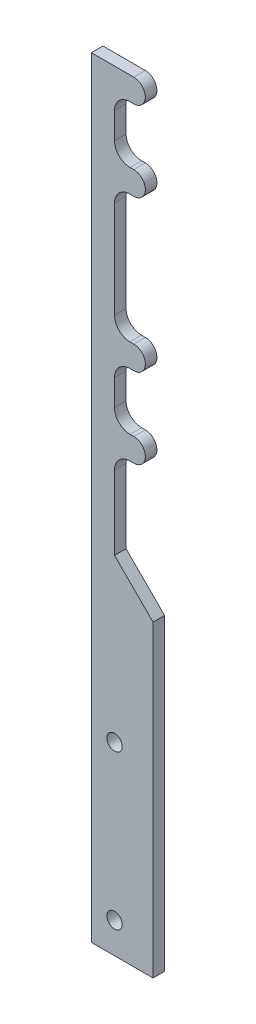
SolidWorks part; units mm, degrees
material "3003 Alloy"
ref_plane "Front Plane" through (0, 0, 0) normal (0, 0, 1) x (1, 0, 0)
ref_plane "Top Plane" through (0, 0, 0) normal (0, 1, 0) x (1, 0, 0)
ref_plane "Right Plane" through (0, 0, 0) normal (1, 0, 0) x (0, 0, -1)
sketch "Sketch1" plane through (0, 0, 0) normal (0, 0, 1) x (1, 0, 0)
  line L0 (0, -45) -> (0, 0) construction
  line L1 (4.5, -15) -> (4.5, -45) construction
  line L2 (-3, -11.6459) -> (-3, -48.3541) construction
  line L3 (-3, -11.3038) -> (-5.5, -11.3038)
  line L4 (-5.5, -11.3038) -> (-5.5, -18.6962)
  line L5 (-5.5, -18.6962) -> (-3, -18.6962)
  line L6 (-3, -8.3038) -> (-8.5, -8.3038)
  line L7 (-8.5, -8.3038) -> (-8.5, -108.3038)
  line L8 (-8.5, -108.3038) -> (-0.5, -108.3038)
  line L9 (-0.5, -108.3038) -> (-0.5, -68.3038)
  line L10 (-0.5, -68.3038) -> (-5.5, -63.3038)
  line L11 (-5.5, -63.3038) -> (-5.5, -51.6962)
  line L12 (-5.5, -51.6962) -> (-3, -51.6962)
  line L13 (-3, -21.6962) -> (-5.5, -21.6962)
  line L14 (-5.5, -21.6962) -> (-5.5, -38.3038)
  line L15 (-3, -38.3038) -> (-5.5, -38.3038)
  line L16 (-3, -41.3038) -> (-5.5, -41.3038)
  line L17 (-5.5, -41.3038) -> (-5.5, -48.6962)
  line L18 (-5.5, -48.6962) -> (-3, -48.6962)
  line L19 (-4.5, -45) -> (-4.5, -72.2595) construction
  circle A0 centre (0, -15) radius 4.5 construction
  circle A1 centre (0, -45) radius 4.5 construction
  circle A2 centre (-3, -20.1962) radius 1.5
  circle A3 centre (-3, -39.8038) radius 1.5
  circle A4 centre (-3, -9.8038) radius 1.5
  circle A5 centre (-3, -50.1962) radius 1.5
  dimension "D3" = 9
  dimension "D4" = 9
  dimension "D6" = 3
  dimension "D1" = 30
  dimension "D2" = 15
  dimension "D5" = 3
  dimension "D7" = 135
  dimension "D8" = 8
  dimension "D9" = 4
  dimension "D10" = 3
  dimension "D11" = 100
  dimension "D12" = 40
extrude "Boss-Extrude1" add sketch "Sketch1" along normal blind 1.5 contours A5 L18 L17 L16 A3 L15 L14 L13 A2 L5 L4 L3 A4 L6 L7 L8 L9 L10 L11 L12 | A3 | A5 | A4 | A2
fillet "Fillet1" radius 2 7 edges at (-5.5, -51.6962, 0.75) (-5.5, -48.6962, 0.75) (-5.5, -41.3038, 0.75) (-5.5, -38.3038, 0.75) (-5.5, -21.6962, 0.75) (-5.5, -18.6962, 0.75) (-5.5, -11.3038, 0.75)
sketch "Sketch2" plane through (0, 0, 1.5) normal (0, 0, 1) x (1, 0, 0)
  line L0 (-0.5, -104.3038) -> (-8.5, -104.3038) construction
  line L1 (-8.5, -8.3038) -> (-8.5, -108.3038) construction
  line L2 (-0.5, -108.3038) -> (-0.5, -68.3038) construction
  line L3 (-8.5, -108.3038) -> (-0.5, -108.3038) construction
  circle A0 centre (-5.5, -104.3038) radius 1
  circle A1 centre (-5.5, -84.3038) radius 1
  dimension "D1" = 2
  dimension "D2" = 2
  dimension "D3" = 20
  dimension "D4" = 4
  dimension "D5" = 5
extrude "Cut-Extrude1" cut sketch "Sketch2" against normal blind 5
